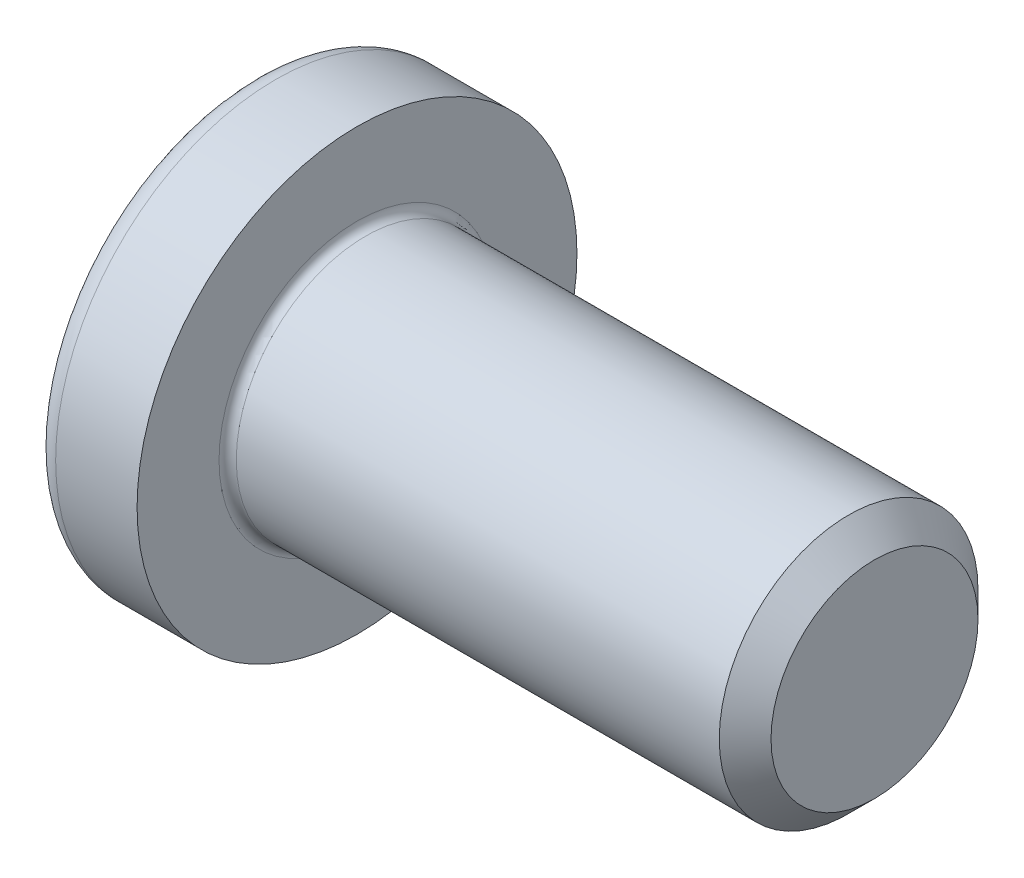
SolidWorks part; units mm, degrees
material "Acier allié"
ref_plane "Plane1" through (0, 0, 0) normal (0, 0, 1) x (1, 0, 0)
ref_plane "Plane2" through (0, 0, 0) normal (0, 1, 0) x (1, 0, 0)
ref_plane "Plane3" through (0, 0, 0) normal (1, 0, 0) x (0, 0, -1)
sketch "BodySke" plane through (0, 0, 0) normal (0, 0, 1) x (1, 0, 0)
  line L0 (1.8, 1.5) -> (1.8, 2.55)
  line L1 (2.05, 6.35) -> (2.05, -3.175) construction
  line L2 (-25.4, 0) -> (127, 0) construction
  line L3 (7.8, 0) -> (0, 0)
  line L4 (1.8, 1.5) -> (7.8, 1.5)
  line L5 (7.8, 1.5) -> (7.8, 0)
  line L6 (0.8558, 2.55) -> (1.8, 2.55)
  line L8 (1.8, 6.35) -> (1.8, -3.175) construction
  arc A0 (0.6192, 2.4101) -> (0, 0) centre (5, 0) ccw
  arc A2 (0.6192, 2.4101) -> (0.8558, 2.55) centre (0.8558, 2.28) cw
  dimension "Head_crown_rad" = 5
  dimension "Head_fillet_rad" = 0.27
  dimension "Length" = 6
  dimension "Head_ht" = 1.8
  dimension "Head_dia" = 5.1
  dimension "Advance" = 0.5
  dimension "Thread_nom" = 6
  dimension "Diameter" = 3
revolve "Base-Revolve" add sketch "BodySke" angle 360 about L2
cosmetic thread "ThreadCosmetic" parameters "Thread_length"=5, "Thread_minor"=2.439
fillet "Fillet1" radius 0.1 1 edges at (1.8, 0, 1.5)
sketch "Sketch3" plane through (0, 0, 0) normal (1, 0, 0) x (0, 0, -1)
  line L0 (0.45, -1.75) -> (-0.45, -1.75)
  line L1 (0.45, -1.75) -> (0.45, 1.75)
  line L2 (-0.45, 1.75) -> (0.45, 1.75)
  line L3 (-0.45, 1.75) -> (-0.45, -1.75)
  dimension "Cross_dia" = 3.5
  dimension "D1" = 1.75
  dimension "Cross_width" = 0.9
  dimension "D2" = 0.45
ref_plane "Plane4" through (1.75, 0, 0) normal (1, 0, 0) x (0, 0, -1)
sketch "Sketch4" plane through (1.75, 0, 0) normal (1, 0, 0) x (0, 0, -1)
  line L0 (0.45, -0.8775) -> (-0.45, -0.8775)
  line L1 (0.45, -0.8775) -> (0.45, 0.8775)
  line L2 (-0.45, 0.8775) -> (0.45, 0.8775)
  line L3 (-0.45, 0.8775) -> (-0.45, -0.8775)
  dimension "D1" = 0.9
  dimension "D2" = 1.755
  dimension "D3" = 0.45
  dimension "D4" = 0.8775
loft "Recess" cut profiles "Sketch3", "Sketch4"
pattern_circular "RecPat" count 2 every 90 about axis through (0, 0, 0) along (1, 0, 0) of "Recess"
sketch "RecCorSke" plane through (0, 0, 0) normal (0, 0, 1) x (1, 0, 0)
  line L0 (-3.175, 0) -> (15.875, 0) construction
  line L1 (-25.4, 0) -> (127, 0) construction
  line L2 (0, 0) -> (0, 0.6784)
  line L3 (0, 0.6784) -> (1.75, 0.556)
  line L4 (1.75, 0.556) -> (1.9307, 0)
  line L5 (1.9307, 0) -> (0, 0)
  dimension "Diameter" = 1.112
  dimension "Depth" = 1.75
  dimension "Draft_angle" = 4
  dimension "Bottom_angle" = 18
revolve "RecessCore" cut sketch "RecCorSke" angle 360 about L0
sketch "ThdSchSke" plane through (0, 0, 0) normal (0, 0, 1) x (1, 0, 0)
  line L0 (2.8, -1.2195) -> (2.6036, -1.5)
  line L1 (2.8, -1.2195) -> (2.9964, -1.5)
  line L2 (2.9964, -1.5) -> (2.9964, -1.875)
  line L3 (-3.175, 0) -> (5.1513, 0) construction
  line L5 (2.9964, -1.875) -> (2.6036, -1.875)
  line L6 (2.6036, -1.875) -> (2.6036, -1.5)
  dimension "Diameter" = 3
  dimension "SideAngle" = 55
  dimension "VeeAngle" = 70
  dimension "Thread_minor" = 2.439
  dimension "Overcut" = 3.75
  dimension "Start" = 2.8
revolve "ThreadSchematic" [suppressed] cut sketch "ThdSchSke" angle 360 about L3
pattern_linear "ThdSchPat" [suppressed]
chamfer "Chanfrein1" distance 0.3 angle 45 1 edges at (7.8, 0, 1.5)
equation "\"D1@Sketch3\" = \"Cross_dia@Sketch3\" / 2"
equation "\"D2@Sketch3\" = \"Cross_width@Sketch3\" / 2"
equation "\"Depth@RecCorSke\" = \"Cross_depth@Plane4\""
equation "\"D1@Sketch4\" = \"Cross_width@Sketch3\""
equation "\"D2@Sketch4\" = \"Cross_dia@Sketch3\" - 2.0 * \"Cross_depth@Plane4\" * tan(26.5  * 0.017453292)"
equation "\"D3@Sketch4\" = \"D1@Sketch4\" / 2"
equation "\"D4@Sketch4\" = \"D2@Sketch4\" / 2"
equation "\"Thread_length@ThreadCosmetic\" = ((sgn( (\"Length@BodySke\" - \"Advance@BodySke\" * 2.0 ) - \"Thread_nom@BodySke\" )-1)*( (\"Length@BodySke\" - \"Advance@BodySke\" * 2.0 ) - \"Thread_nom@BodySke\" ))/-2+ \"Thread_nom@BodySke\""
equation "\"Thread_minor@ThdSchSke\" = \"Thread_minor@ThreadCosmetic\""
equation "\"Diameter@ThdSchSke\" = \"Diameter@BodySke\""
equation "\"Overcut@ThdSchSke\" = \"Diameter@BodySke\" * 1.25"
equation "\"Start@ThdSchSke\" = \"Head_ht@BodySke\" + \"Length@BodySke\" - \"Thread_length@ThreadCosmetic\"  '---Non-countersunk---"
equation "\"Num_threads@ThdSchPat\" = int( \"Thread_length@ThreadCosmetic\" / \"Advance@BodySke\" + 0.999 )  + 1"
equation "\"Advance@ThdSchPat\" = \"Thread_length@ThreadCosmetic\" /  (\"Num_threads@ThdSchPat\" - 1) 'relax it"
